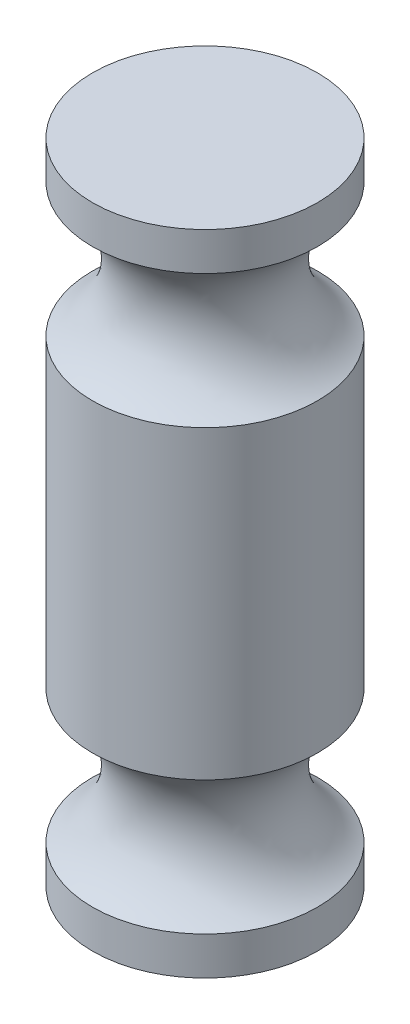
SolidWorks part; units mm, degrees
ref_plane "前视基准面" through (0, 0, 0) normal (0, 0, 1) x (1, 0, 0)
ref_plane "上视基准面" through (0, 0, 0) normal (0, 1, 0) x (1, 0, 0)
ref_plane "右视基准面" through (0, 0, 0) normal (1, 0, 0) x (0, 0, -1)
sketch "草图1" plane through (0, 0, 0) normal (0, 0, 1) x (1, 0, 0)
  line L0 (0, 0) -> (0, 8.56)
  line L1 (0, 8.56) -> (2.95, 8.56)
  line L2 (2.95, 8.56) -> (2.95, 7.56)
  line L3 (2.95, 4.06) -> (2.95, -3.94)
  line L4 (2.95, -7.44) -> (2.95, -8.44)
  line L5 (2.95, -8.44) -> (0, -8.44)
  line L6 (0, -8.44) -> (0, 0)
  arc A0 (2.95, 7.56) -> (2.95, 4.06) centre (3.9182, 5.81) ccw
  arc A1 (2.95, -3.94) -> (2.95, -7.44) centre (3.9182, -5.69) ccw
  dimension "D6" = 2
  dimension "D8" = 2
  dimension "D7" = 3.5
  dimension "D1" = 2.95
  dimension "D2" = 1
  dimension "D3" = 1
  dimension "D4" = 17
  dimension "D5" = 8.56
  dimension "D9" = 3.5
  dimension "D10" = 8
revolve "旋转1" add sketch "草图1" angle 360 about L6
